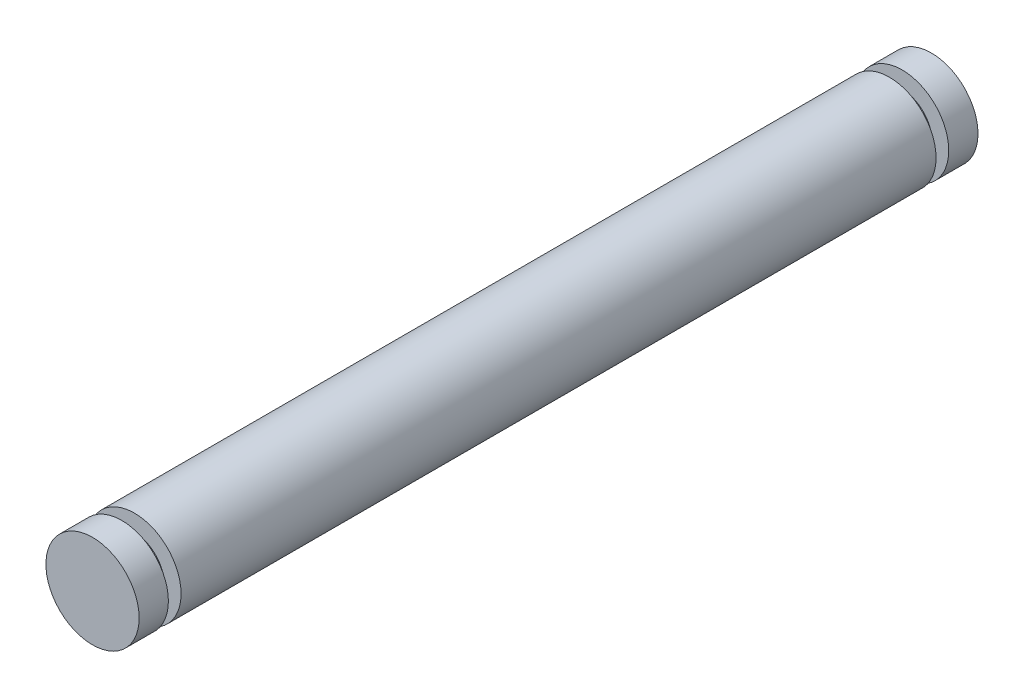
SolidWorks part; units mm, degrees
ref_plane "Front Plane" through (0, 0, 0) normal (0, 0, 1) x (1, 0, 0)
ref_plane "Top Plane" through (0, 0, 0) normal (0, 1, 0) x (1, 0, 0)
ref_plane "Right Plane" through (0, 0, 0) normal (1, 0, 0) x (0, 0, -1)
sketch "Sketch1" plane through (0, 0, 0) normal (0, 0, 1) x (1, 0, 0)
  circle A0 centre (0, 0) radius 2.5
  dimension "D1" = 5
extrude "Boss-Extrude1" add sketch "Sketch1" against normal blind 45
sketch "Sketch2" plane through (0, 0, 0) normal (1, 0, 0) x (0, 0, -1)
  line L0 (0, 2.5) -> (1.57, 2.5) construction
  line L1 (45, 2.5) -> (0, 2.5) construction
  line L2 (1.57, 2.5) -> (1.57, 1.6)
  line L3 (1.57, 1.6) -> (2.25, 1.6)
  line L4 (2.25, 1.6) -> (2.25, 2.5)
  line L5 (2.25, 2.5) -> (1.57, 2.5)
  line L6 (0, -2.5) -> (1.57, -2.5) construction
  line L7 (0, -2.5) -> (45, -2.5) construction
  line L8 (1.57, -2.5) -> (1.57, -1.6) construction
  line L9 (1.57, -1.6) -> (2.25, -1.6) construction
  line L10 (2.25, -1.6) -> (2.25, -2.5) construction
  line L11 (2.25, -2.5) -> (1.57, -2.5) construction
  line L12 (22.5, 2.5) -> (22.5, -2.5) construction
  line L13 (45, 2.5) -> (43.43, 2.5) construction
  line L14 (42.75, 2.5) -> (43.43, 2.5)
  line L15 (42.75, 1.6) -> (42.75, 2.5)
  line L16 (43.43, 1.6) -> (42.75, 1.6)
  line L17 (43.43, 2.5) -> (43.43, 1.6)
  line L18 (0, 0) -> (45, 0) construction
  line L19 (45, -2.5) -> (45, 2.5) construction
  dimension "D1" = 3.2
  dimension "D2" = 0.68
  dimension "D3" = 2.25
revolve "Cut-Revolve1" cut sketch "Sketch2" angle 360 about L18
